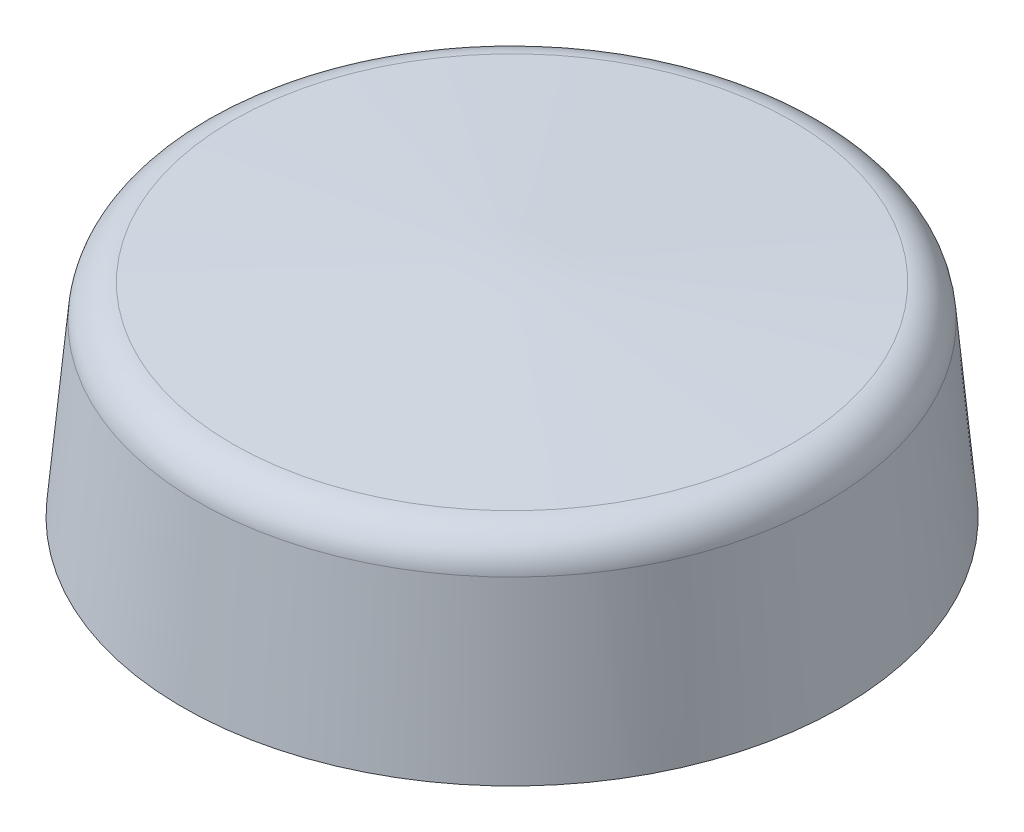
SolidWorks part; units mm, degrees
ref_plane "Front Plane" through (0, 0, 0) normal (0, 0, 1) x (1, 0, 0)
ref_plane "Top Plane" through (0, 0, 0) normal (0, 1, 0) x (1, 0, 0)
ref_plane "Right Plane" through (0, 0, 0) normal (1, 0, 0) x (0, 0, -1)
sketch "Sketch1" plane through (0, 0, 0) normal (0, 0, 1) x (1, 0, 0)
  line L0 (0, -102.3274) -> (0, 5014.0424) construction
  line L3 (4.5, 0) -> (0, 0)
  line L4 (0, 0) -> (0, 3)
  line L5 (0, 3) -> (4.25, 2.75)
  line L6 (4.25, 2.75) -> (4.5, 0)
  dimension "D1" = 9
  dimension "D2" = 3
  dimension "D3" = 0.25
  dimension "D4" = 0.25
revolve "Revolve1" add sketch "Sketch1" angle 360 about L0
fillet "Fillet1" radius 0.5 1 edges at (4.25, 2.75, 0)
